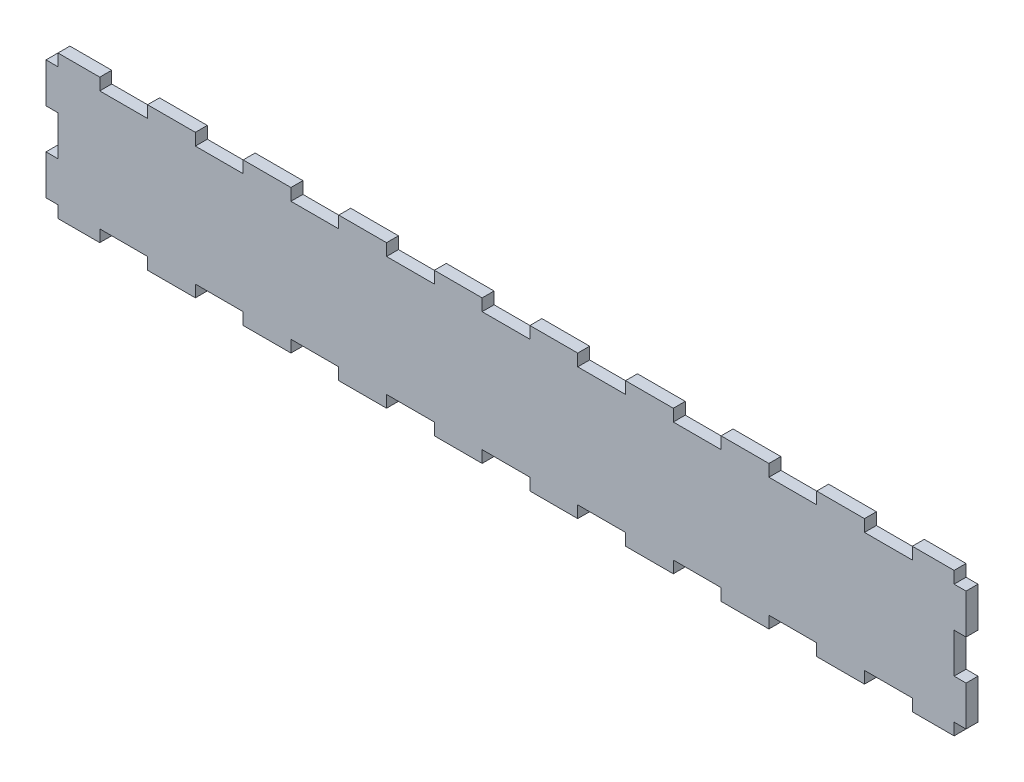
SolidWorks part; units mm, degrees
ref_plane "Front Plane" through (0, 0, 0) normal (0, 0, 1) x (1, 0, 0)
ref_plane "Top Plane" through (0, 0, 0) normal (0, 1, 0) x (1, 0, 0)
ref_plane "Right Plane" through (0, 0, 0) normal (1, 0, 0) x (0, 0, -1)
sketch "Sketch1" plane through (0, 0, 0) normal (0, 0, 1) x (1, 0, 0)
  line L0 (-225, 6) -> (-204, 6)
  line L1 (-204, 6) -> (-204, 0)
  line L2 (-204, 0) -> (-180, 0)
  line L3 (-180, 0) -> (-180, 6)
  line L4 (-180, 6) -> (-156, 6)
  line L5 (-156, 6) -> (-156, 0)
  line L6 (-156, 0) -> (-132, 0)
  line L7 (-132, 0) -> (-132, 6)
  line L8 (-132, 6) -> (-108, 6)
  line L9 (-108, 6) -> (-108, 0)
  line L10 (-108, 0) -> (-84, 0)
  line L11 (-84, 0) -> (-84, 6)
  line L12 (-84, 6) -> (-60, 6) construction
  line L13 (-84, 6) -> (-60, 6)
  line L14 (-60, 6) -> (-60, 0)
  line L15 (-60, 0) -> (-36, 0)
  line L16 (-36, 0) -> (-36, 6)
  line L17 (-36, 6) -> (-12, 6)
  line L18 (-12, 6) -> (-12, 0)
  line L19 (-12, 0) -> (12, 0)
  line L20 (12, 0) -> (12, 6)
  line L21 (12, 6) -> (36, 6)
  line L22 (36, 6) -> (36, 0)
  line L23 (36, 0) -> (60, 0)
  line L24 (60, 0) -> (60, 6)
  line L25 (60, 6) -> (84, 6)
  line L26 (84, 6) -> (84, 0)
  line L27 (84, 0) -> (108, 0)
  line L28 (108, 0) -> (108, 6)
  line L29 (108, 6) -> (132, 6)
  line L30 (132, 6) -> (132, 0)
  line L31 (132, 0) -> (156, 0)
  line L32 (156, 0) -> (156, 6)
  line L33 (156, 6) -> (180, 6)
  line L34 (180, 6) -> (180, 0)
  line L35 (180, 0) -> (204, 0)
  line L36 (204, 0) -> (204, 6)
  line L37 (204, 6) -> (225, 6)
  line L38 (-225, 6) -> (-225, 66)
  line L39 (225, 6) -> (225, 66)
  line L40 (-225, 6) -> (-225, 0)
  line L78 (-225, 0) -> (225, 0)
  line L79 (225, 0) -> (225, 6)
  line L80 (-225, 6) -> (225, 6)
  line L81 (-225, 36) -> (225, 36)
  line L82 (-225, 66) -> (225, 66)
  line L83 (225, 72) -> (225, 66)
  line L84 (-225, 72) -> (225, 72)
  line L85 (-225, 66) -> (-225, 72)
  line L86 (204, 66) -> (225, 66)
  line L87 (204, 72) -> (204, 66)
  line L88 (180, 72) -> (204, 72)
  line L89 (180, 66) -> (180, 72)
  line L90 (156, 66) -> (180, 66)
  line L91 (156, 72) -> (156, 66)
  line L92 (132, 72) -> (156, 72)
  line L93 (132, 66) -> (132, 72)
  line L94 (108, 66) -> (132, 66)
  line L95 (108, 72) -> (108, 66)
  line L96 (84, 72) -> (108, 72)
  line L97 (84, 66) -> (84, 72)
  line L98 (60, 66) -> (84, 66)
  line L99 (60, 72) -> (60, 66)
  line L100 (36, 72) -> (60, 72)
  line L101 (36, 66) -> (36, 72)
  line L102 (12, 66) -> (36, 66)
  line L103 (12, 72) -> (12, 66)
  line L104 (-12, 72) -> (12, 72)
  line L105 (-12, 66) -> (-12, 72)
  line L106 (-36, 66) -> (-12, 66)
  line L107 (-36, 72) -> (-36, 66)
  line L108 (-60, 72) -> (-36, 72)
  line L109 (-60, 66) -> (-60, 72)
  line L110 (-84, 66) -> (-60, 66)
  line L111 (-84, 72) -> (-84, 66)
  line L112 (-108, 72) -> (-84, 72)
  line L113 (-108, 66) -> (-108, 72)
  line L114 (-132, 66) -> (-108, 66)
  line L115 (-132, 72) -> (-132, 66)
  line L116 (-156, 72) -> (-132, 72)
  line L117 (-156, 66) -> (-156, 72)
  line L118 (-180, 66) -> (-156, 66)
  line L119 (-180, 72) -> (-180, 66)
  line L120 (-204, 72) -> (-180, 72)
  line L121 (-204, 66) -> (-204, 72)
  line L122 (-225, 66) -> (-204, 66)
extrude "Boss-Extrude1" add sketch "Sketch1" along normal blind 6
sketch "Sketch3" plane through (0, 0, 6) normal (0, 0, 1) x (1, 0, 0)
  line L0 (-225, 0) -> (-225, 72) construction
  line L1 (-225, 6) -> (-231, 6)
  line L2 (-225, 6) -> (-225, 26)
  line L3 (-225, 26) -> (-231, 26)
  line L4 (-231, 6) -> (-231, 26)
  line L5 (-225, 46) -> (-225, 66)
  line L6 (-225, 46) -> (-231, 46)
  line L7 (-231, 46) -> (-231, 66)
  line L8 (-225, 66) -> (-231, 66)
  line L9 (-225, 46) -> (-225, 26)
  line L10 (231, 6) -> (231, 26)
  line L11 (231, 6) -> (225, 6)
  line L12 (225, 6) -> (225, 26)
  line L13 (231, 26) -> (225, 26)
  line L14 (231, 46) -> (231, 66)
  line L15 (231, 46) -> (225, 46)
  line L16 (225, 46) -> (225, 66)
  line L17 (231, 66) -> (225, 66)
  line L18 (225, 0) -> (225, 72) construction
  point P7 (-225, 36)
  dimension "D1" = 20
  dimension "D4" = 6
  dimension "D5" = 20
  dimension "D6" = 6
  dimension "D2" = 2
  dimension "D3" = 2
extrude "Boss-Extrude2" add sketch "Sketch3" against normal blind 6 contours L6 L7 L8 L5 | L2 L1 L4 L3 | L16 L17 L14 L15 | L12 L13 L10 L11
